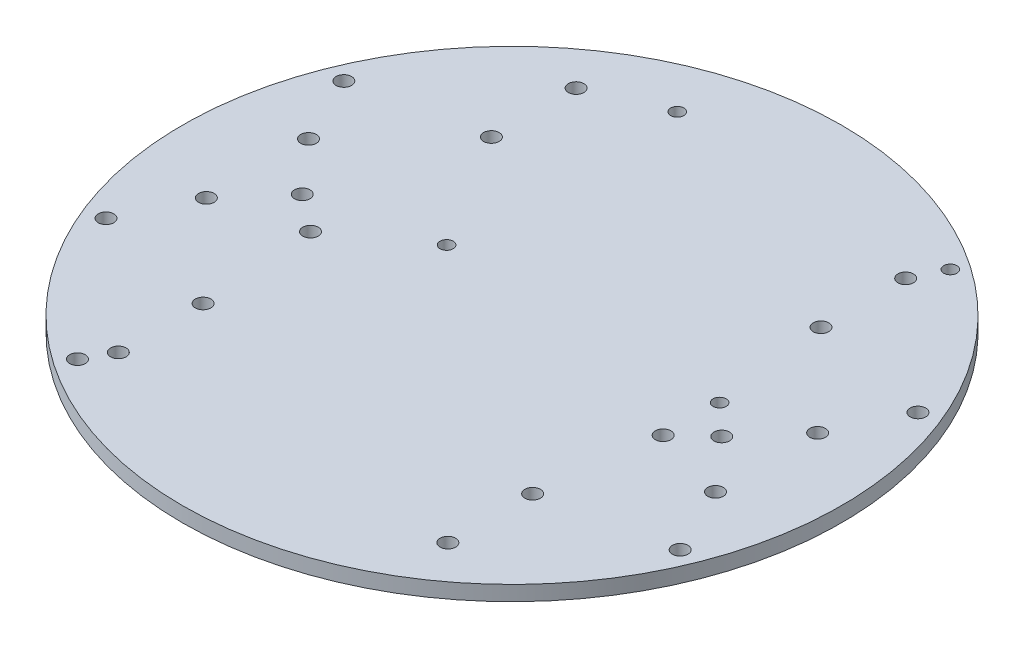
SolidWorks part; units mm, degrees
ref_plane "Front Plane" through (0, 0, 0) normal (0, 0, 1) x (1, 0, 0)
ref_plane "Top Plane" through (0, 0, 0) normal (0, 1, 0) x (1, 0, 0)
ref_plane "Right Plane" through (0, 0, 0) normal (1, 0, 0) x (0, 0, -1)
sketch "Base w/ Motor Mounts" plane through (0, 0, 0) normal (0, 1, 0) x (1, 0, 0)
  line L0 (0, 70) -> (0, -70) construction
  line L1 (0, 0) -> (70, 0) construction
  circle A0 centre (0, 0) radius 70
  circle A1 centre (44.55, 0) radius 1.651
  circle A2 centre (54.075, 10.85) radius 1.651
  circle A3 centre (54.075, -10.85) radius 1.651
  circle A4 centre (-54.075, -10.85) radius 1.651
  circle A5 centre (-54.075, 10.85) radius 1.651
  circle A6 centre (-44.55, 0) radius 1.651
  dimension "D1" = 3.302
  dimension "D6" = 140
  dimension "D2" = 21.7
  dimension "D3" = 10.85
  dimension "D4" = 15.925
  dimension "D5" = 9.525
sketch "Standoffs (top / bottom)" plane through (0, 0, 0) normal (0, 1, 0) x (1, 0, 0)
  line L0 (0, 0) -> (64.6716, 26.7878) construction
  line L1 (0, 0) -> (49.4975, 49.4975) construction
  line L2 (0, 0) -> (26.7878, 64.6716) construction
  line L3 (0, 0) -> (70, 0) construction
  line L4 (-70, 0) -> (70, 0) construction
  line L5 (0, 0) -> (64.6716, -26.7878) construction
  line L6 (0, 0) -> (49.4975, -49.4975) construction
  line L7 (0, 0) -> (26.7878, -64.6716) construction
  line L8 (0, 70) -> (0, -70) construction
  line L9 (0, 0) -> (-26.7878, -64.6716) construction
  line L10 (0, 0) -> (-49.4975, -49.4975) construction
  line L11 (0, 0) -> (-64.6716, -26.7878) construction
  line L12 (0, 0) -> (-26.7878, 64.6716) construction
  line L13 (0, 0) -> (-49.4975, 49.4975) construction
  line L14 (0, 0) -> (-64.6716, 26.7878) construction
  line L15 (35, 60.6218) -> (35, 0) construction
  circle A0 centre (0, 0) radius 70 construction
  circle A3 centre (60.976, 25.2571) radius 1.65
  circle A6 centre (60.976, -25.2571) radius 1.65
  circle A9 centre (-60.976, -25.2571) radius 1.65
  circle A12 centre (-60.976, 25.2571) radius 1.65
  circle A14 centre (0, 0) radius 70 construction
  circle A15 centre (35, 48.6218) radius 1.65
  circle A16 centre (35, 30.6218) radius 1.65
  circle A17 centre (35, -30.6218) radius 1.65
  circle A18 centre (35, -48.6218) radius 1.65
  circle A19 centre (-35, -48.6218) radius 1.65
  circle A20 centre (-35, -30.6218) radius 1.65
  circle A21 centre (-35, 30.6218) radius 1.65
  circle A22 centre (-35, 48.6218) radius 1.65
  dimension "D4" = 3.3
  dimension "D5" = 35
  dimension "D6" = 12
  dimension "D1" = 22.5
  dimension "D2" = 22.5
  dimension "D3" = 22.5
  dimension "D7" = 18
sketch "Pi and Mega Standoffs" plane through (0, 0, 0) normal (0, 1, 0) x (1, 0, 0)
  line L0 (0, 70) -> (0, -70) construction
  line L1 (-19.9, 55) -> (38.1, 55) construction
  line L2 (-19.9, 55) -> (-19.9, 6) construction
  line L3 (-19.9, 6) -> (38.1, 6) construction
  line L4 (38.1, 55) -> (38.1, 6) construction
  line L5 (-19.9, 55) -> (38.1, 6) construction
  line L6 (-19.9, 6) -> (38.1, 55) construction
  line L7 (0, 0) -> (70, 0) construction
  line L8 (-38.1, -6) -> (38.1, -6) construction
  line L9 (-38.1, -6) -> (-38.1, -54.2) construction
  line L10 (-38.1, -54.2) -> (38.1, -54.2) construction
  line L11 (38.1, -6) -> (38.1, -54.2) construction
  line L12 (-38.1, -6) -> (38.1, -54.2) construction
  line L13 (-38.1, -54.2) -> (38.1, -6) construction
  circle A0 centre (-19.9, 55) radius 1.4
  circle A1 centre (38.1, 55) radius 1.4
  circle A2 centre (38.1, 6) radius 1.4
  circle A3 centre (-19.9, 6) radius 1.4
  circle A4 centre (-38.1, -54.2) radius 1.65
  circle A5 centre (-36.8, -6) radius 1.65
  circle A6 centre (38.1, -6) radius 1.65
  point P0 (-10.6204, 31.3097)
  point P11 (0, -30.1)
  dimension "D3" = 2.8
  dimension "D5" = 3.3
  dimension "D1" = 49
  dimension "D2" = 58
  dimension "D4" = 76.2
  dimension "D6" = 1.3
  dimension "D7" = 74.9
  dimension "D8" = 48.2
  dimension "D9" = 6
extrude "Boss-Extrude1" add sketch "Base w/ Motor Mounts" along normal blind 3.175
extrude "Cut-Extrude2" cut sketch "Standoffs (top / bottom)" along normal blind 3.175
extrude "Cut-Extrude3" cut sketch "Pi and Mega Standoffs" along normal blind 3.175
